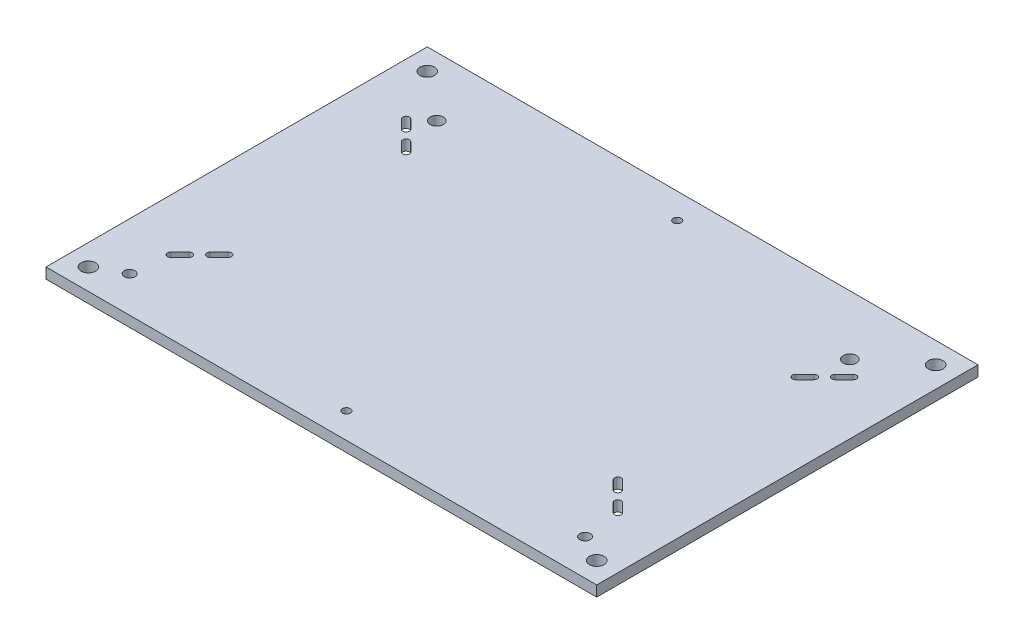
SolidWorks part; units mm, degrees
ref_plane "Front Plane" through (0, 0, 0) normal (0, 0, 1) x (1, 0, 0)
ref_plane "Top Plane" through (0, 0, 0) normal (0, 1, 0) x (1, 0, 0)
ref_plane "Right Plane" through (0, 0, 0) normal (1, 0, 0) x (0, 0, -1)
sketch "Sketch1" plane through (0, 0, 0) normal (0, 1, 0) x (1, 0, 0)
  line L1 (0, 0) -> (330.2, 0)
  line L2 (0, 0) -> (0, -228.6)
  line L3 (0, -228.6) -> (330.2, -228.6)
  line L4 (330.2, 0) -> (330.2, -228.6)
  dimension "D1" = 330.2
  dimension "D2" = 228.6
extrude "base plate" add sketch "Sketch1" against normal blind 6.35
sketch "center lines" plane through (0, 0, 0) normal (0, 1, 0) x (1, 0, 0)
  line L0 (165.1, 0) -> (165.1, -228.6) construction
  line L1 (330.2, 0) -> (0, 0) construction
  line L2 (0, -228.6) -> (330.2, -228.6) construction
  line L3 (0, -114.3) -> (330.2, -114.3) construction
  line L4 (0, 0) -> (0, -228.6) construction
  line L5 (330.2, -228.6) -> (330.2, 0) construction
sketch "Sketch3" plane through (0, 0, 0) normal (0, 1, 0) x (1, 0, 0)
  line L0 (21.0672, -185.8525) -> (30.0475, -194.8328)
  line L1 (30.0475, -194.8328) -> (60.5804, -164.2999)
  line L2 (60.5804, -164.2999) -> (51.6001, -155.3196)
  line L3 (51.6001, -155.3196) -> (21.0672, -185.8525)
  line L4 (31.0806, -184.8194) -> (36.4687, -179.4313) construction
  line L5 (29.6664, -183.4052) -> (35.0545, -178.0171)
  line L6 (32.4948, -186.2336) -> (37.8829, -180.8455)
  line L7 (0, -228.6) -> (330.2, -228.6) construction
  line L8 (48.2774, -167.6226) -> (42.8893, -173.0107) construction
  line L9 (49.6916, -169.0368) -> (44.3035, -174.425)
  line L10 (165.1, 0) -> (165.1, -228.6) construction
  line L11 (0, -114.3) -> (330.2, -114.3) construction
  line L12 (60.5804, -64.3001) -> (51.6001, -73.2804)
  line L13 (30.0475, -33.7672) -> (60.5804, -64.3001)
  line L14 (21.0672, -42.7475) -> (30.0475, -33.7672)
  line L15 (51.6001, -73.2804) -> (21.0672, -42.7475)
  line L16 (300.1525, -33.7672) -> (269.6196, -64.3001)
  line L17 (309.1328, -42.7475) -> (300.1525, -33.7672)
  line L18 (278.5999, -73.2804) -> (309.1328, -42.7475)
  line L19 (269.6196, -64.3001) -> (278.5999, -73.2804)
  line L20 (269.6196, -164.2999) -> (278.5999, -155.3196)
  line L21 (300.1525, -194.8328) -> (269.6196, -164.2999)
  line L22 (309.1328, -185.8525) -> (300.1525, -194.8328)
  line L23 (278.5999, -155.3196) -> (309.1328, -185.8525)
  line L24 (46.8632, -166.2084) -> (41.475, -171.5965)
  line L25 (31.0806, -43.7806) -> (36.4687, -49.1687) construction
  line L26 (29.6664, -45.1948) -> (35.0545, -50.5829)
  line L27 (32.4948, -42.3664) -> (37.8829, -47.7545)
  line L28 (48.2774, -60.9774) -> (42.8893, -55.5893) construction
  line L29 (49.6916, -59.5632) -> (44.3035, -54.175)
  line L30 (46.8632, -62.3916) -> (41.475, -57.0035)
  line L31 (299.1194, -43.7806) -> (293.7313, -49.1687) construction
  line L32 (300.5336, -45.1948) -> (295.1455, -50.5829)
  line L33 (297.7052, -42.3664) -> (292.3171, -47.7545)
  line L34 (281.9226, -60.9774) -> (287.3107, -55.5893) construction
  line L35 (280.5084, -59.5632) -> (285.8965, -54.175)
  line L36 (283.3368, -62.3916) -> (288.725, -57.0035)
  line L37 (281.9226, -167.6226) -> (287.3107, -173.0107) construction
  line L38 (280.5084, -169.0368) -> (285.8965, -174.425)
  line L39 (283.3368, -166.2084) -> (288.725, -171.5965)
  line L40 (299.1194, -184.8194) -> (293.7313, -179.4313) construction
  line L41 (300.5336, -183.4052) -> (295.1455, -178.0171)
  line L42 (297.7052, -186.2336) -> (292.3171, -180.8455)
  line L43 (51.6001, -164.2999) -> (51.6001, -155.3196)
  line L44 (60.5804, -164.2999) -> (51.6001, -164.2999)
  line L45 (51.6001, -64.3001) -> (51.6001, -73.2804)
  line L46 (60.5804, -64.3001) -> (51.6001, -64.3001)
  line L47 (278.5999, -64.3001) -> (278.5999, -73.2804)
  line L48 (269.6196, -64.3001) -> (278.5999, -64.3001)
  line L49 (278.5999, -164.2999) -> (278.5999, -155.3196)
  line L50 (269.6196, -164.2999) -> (278.5999, -164.2999)
  arc A0 (29.6664, -183.4052) -> (32.4948, -186.2336) centre (31.0806, -184.8194) ccw
  arc A1 (37.8829, -180.8455) -> (35.0545, -178.0171) centre (36.4687, -179.4313) ccw
  arc A2 (49.6916, -169.0368) -> (46.8632, -166.2084) centre (48.2774, -167.6226) ccw
  arc A3 (41.475, -171.5965) -> (44.3035, -174.425) centre (42.8893, -173.0107) ccw
  arc A4 (29.6664, -45.1948) -> (32.4948, -42.3664) centre (31.0806, -43.7806) cw
  arc A5 (37.8829, -47.7545) -> (35.0545, -50.5829) centre (36.4687, -49.1687) cw
  arc A6 (49.6916, -59.5632) -> (46.8632, -62.3916) centre (48.2774, -60.9774) cw
  arc A7 (41.475, -57.0035) -> (44.3035, -54.175) centre (42.8893, -55.5893) cw
  arc A8 (300.5336, -45.1948) -> (297.7052, -42.3664) centre (299.1194, -43.7806) ccw
  arc A9 (292.3171, -47.7545) -> (295.1455, -50.5829) centre (293.7313, -49.1687) ccw
  arc A10 (280.5084, -59.5632) -> (283.3368, -62.3916) centre (281.9226, -60.9774) ccw
  arc A11 (288.725, -57.0035) -> (285.8965, -54.175) centre (287.3107, -55.5893) ccw
  arc A12 (280.5084, -169.0368) -> (283.3368, -166.2084) centre (281.9226, -167.6226) cw
  arc A13 (288.725, -171.5965) -> (285.8965, -174.425) centre (287.3107, -173.0107) cw
  arc A14 (300.5336, -183.4052) -> (297.7052, -186.2336) centre (299.1194, -184.8194) cw
  arc A15 (292.3171, -180.8455) -> (295.1455, -178.0171) centre (293.7313, -179.4313) cw
  point P29 (33.7746, -182.1254)
  point P36 (45.5833, -170.3167)
  point P44 (33.7746, -46.4746)
  point P51 (45.5833, -58.2833)
  point P58 (296.4254, -46.4746)
  point P65 (284.6167, -58.2833)
  point P72 (284.6167, -170.3167)
  point P79 (296.4254, -182.1254)
  point P84 (37.8829, -178.0171)
  point P85 (41.475, -174.425)
  dimension "D6" = 2
  dimension "D10" = 5.08
  dimension "D9" = 4.699
  dimension "D1" = 43.18
  dimension "D2" = 12.7
  dimension "D3" = 45
  dimension "D4" = 99.9998
  dimension "D5" = 226.9998
  dimension "D7" = 7.62
  dimension "D8" = 6.35
extrude "slots" cut sketch "Sketch3" against normal through all contours A5 L27 A4 L26 | L33 A9 L32 A8 | L36 A11 L35 A10 | A13 L39 A12 L38 | A15 L42 A14 L41 | L6 A1 L5 A0 | L24 A3 L9 A2 | L30 A7 L29 A6
sketch "location of ESD" [suppressed] plane through (0, 0, 0) normal (0, 1, 0) x (1, 0, 0)
  line L0 (330.2, -228.6) -> (330.2, 0) construction
  line L1 (330.2, 0) -> (0, 0) construction
  point P0 (304.8, -114.3)
  point P3 (330.2, -114.3)
  dimension "D1" = 25.4
  dimension "D2" = 114.3
hole_wizard "Feet connection hole" positions "Sketch6" profile "Sketch7" hole size "1/4-20" standard "PEM® Inch" end condition through all
sketch "Sketch6" plane through (0, 0, 0) normal (0, 1, 0) x (1, 0, 0)
  line L0 (0, -228.6) -> (330.2, -228.6) construction
  line L1 (0, 0) -> (0, -228.6) construction
  line L2 (330.2, -228.6) -> (330.2, 0) construction
  line L3 (330.2, 0) -> (0, 0) construction
  point P3 (12.7, -215.9)
  point P19 (317.5, -12.7)
  point P31 (317.5, -215.9)
  point P33 (12.7, -12.7)
  dimension "D1" = 12.7
  dimension "D2" = 12.7
  dimension "D3" = 12.7
  dimension "D4" = 12.7
sketch "Sketch7" plane through (12.7, 0, 215.9) normal (1, 0, 0) x (0, 0, 1)
  line L0 (0, 0) -> (0, 6.35)
  line L1 (0, 6.35) -> (4.3688, 6.35)
  line L2 (4.3688, 6.35) -> (4.3688, 0)
  line L5 (4.3688, 0) -> (0, 0)
  line L11 (0, -6.35) -> (0, 107.95) construction
  dimension "Thru Hole Dia." = 8.7376
  dimension "Thru Hole Depth" = 6.35
sketch "Vacuum Chamber base hole locations" plane through (0, 0, 0) normal (0, 1, 0) x (1, 0, 0)
  line L2 (330.2, -228.6) -> (330.2, 0) construction
  line L4 (330.2, 0) -> (0, 0) construction
  point P0 (41.275, -35.56)
  point P1 (288.925, -35.56)
  point P2 (301.625, -207.01)
  point P3 (28.575, -207.01)
  dimension "D1" = 247.65
  dimension "D2" = 12.7
  dimension "D3" = 12.7
  dimension "D4" = 171.45
  dimension "D5" = 28.575
  dimension "D6" = 35.56
  dimension "D7" = 0
  dimension "D8" = 171.45
hole_wizard "1/4 (0.25) Diameter Hole1" positions "Sketch9" profile "Sketch10" hole size "1/4" standard "ANSI Inch" end condition through all
sketch "Sketch9" plane through (0, 0, 0) normal (0, 1, 0) x (1, 0, 0)
  point P0 (28.575, -207.01)
  point P3 (301.625, -207.01)
sketch "Sketch10" plane through (28.575, 0, 207.01) normal (1, 0, 0) x (0, 0, 1)
  line L0 (0, 0) -> (0, 6.35)
  line L1 (0, 6.35) -> (3.175, 6.35)
  line L2 (3.175, 6.35) -> (3.175, 0)
  line L5 (3.175, 0) -> (0, 0)
  line L11 (0, -6.35) -> (0, 107.95) construction
  dimension "Thru Hole Dia." = 6.35
  dimension "Thru Hole Depth" = 6.35
hole_wizard "5/16 (0.3125) Diameter Hole1" positions "Sketch11" profile "Sketch12" hole size "5/16" standard "ANSI Inch" end condition through all
sketch "Sketch11" plane through (0, 0, 0) normal (0, 1, 0) x (1, 0, 0)
  point P0 (41.275, -35.56)
  point P3 (288.925, -35.56)
sketch "Sketch12" plane through (41.275, 0, 35.56) normal (1, 0, 0) x (0, 0, 1)
  line L0 (0, 0) -> (0, 6.35)
  line L1 (0, 6.35) -> (3.9687, 6.35)
  line L2 (3.9687, 6.35) -> (3.9687, 0)
  line L5 (3.9687, 0) -> (0, 0)
  line L11 (0, -6.35) -> (0, 107.95) construction
  dimension "Thru Hole Dia." = 7.9375
  dimension "Thru Hole Depth" = 6.35
sketch "Sketch14" plane through (0, 0, 0) normal (0, 1, 0) x (1, 0, 0)
  line L2 (0, 0) -> (0, -228.6) construction
  line L3 (330.2, 0) -> (0, 0) construction
  line L4 (0, -228.6) -> (330.2, -228.6) construction
  point P0 (165.1, -15.24)
  point P1 (165.1, -213.36)
  dimension "D1" = 165.1
  dimension "D2" = 15.24
  dimension "D3" = 165.1
  dimension "D4" = 15.24
hole_wizard "ESD Connection hole" positions "Sketch15" profile "Sketch16" hole size "#6-32" standard "PEM® Inch" end condition through all
sketch "Sketch15" plane through (0, 0, 0) normal (0, 1, 0) x (1, 0, 0)
  point P0 (165.1, -15.24)
  point P3 (164.7687, -213.267)
sketch "Sketch16" plane through (165.1, 0, 15.24) normal (1, 0, 0) x (0, 0, 1)
  line L0 (0, 0) -> (0, 6.35)
  line L1 (0, 6.35) -> (2.3812, 6.35)
  line L2 (2.3812, 6.35) -> (2.3812, 0)
  line L5 (2.3812, 0) -> (0, 0)
  line L11 (0, -6.35) -> (0, 107.95) construction
  dimension "Thru Hole Dia." = 4.7625
  dimension "Thru Hole Depth" = 6.35
